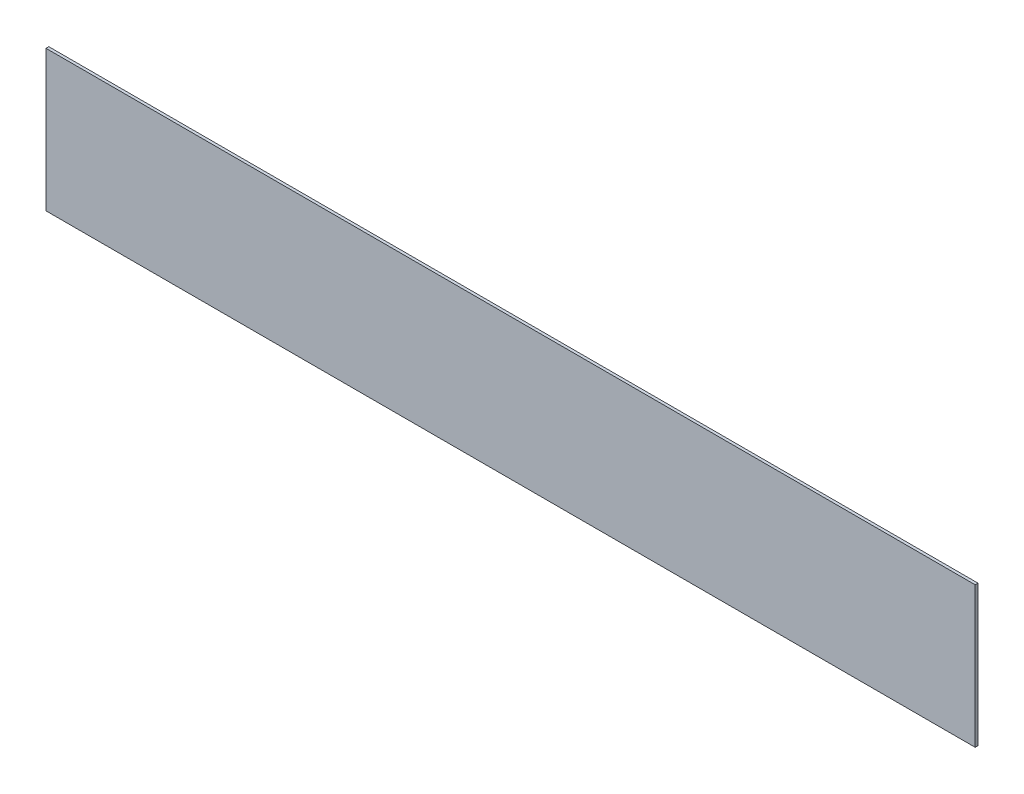
SolidWorks part; units mm, degrees
ref_plane "前视基准面" through (0, 0, 0) normal (0, 0, 1) x (1, 0, 0)
ref_plane "上视基准面" through (0, 0, 0) normal (0, 1, 0) x (1, 0, 0)
ref_plane "右视基准面" through (0, 0, 0) normal (1, 0, 0) x (0, 0, -1)
sketch "草图1" plane through (0, 0, 0) normal (0, 0, 1) x (1, 0, 0)
  line L1 (-16.5, -2.5) -> (16.5, -2.5)
  line L2 (-16.5, -2.5) -> (-16.5, 2.5)
  line L3 (-16.5, 2.5) -> (16.5, 2.5)
  line L4 (16.5, -2.5) -> (16.5, 2.5)
  line L5 (-16.5, -2.5) -> (16.5, 2.5) construction
  line L6 (-16.5, 2.5) -> (16.5, -2.5) construction
  point P0 (0, 0)
  dimension "D1" = 33
  dimension "D2" = 5
extrude "凸台-拉伸1" add sketch "草图1" along normal blind 0.1
